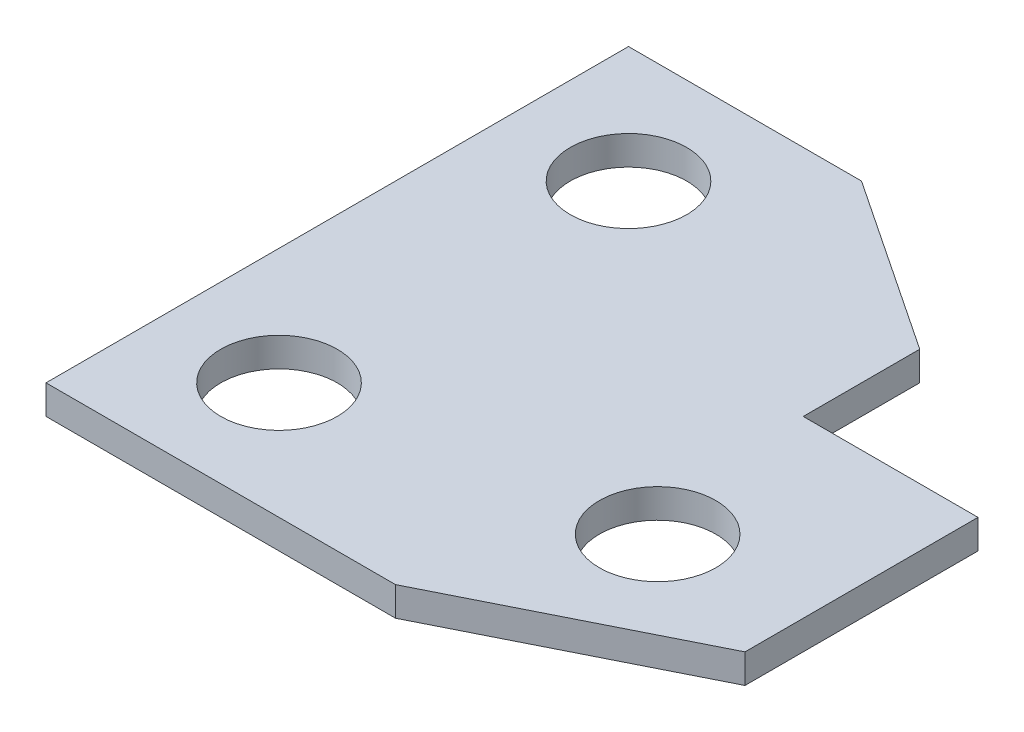
SolidWorks part; units mm, degrees
ref_plane "Front Plane" through (0, 0, 0) normal (0, 0, 1) x (1, 0, 0)
ref_plane "Top Plane" through (0, 0, 0) normal (0, 1, 0) x (1, 0, 0)
ref_plane "Right Plane" through (0, 0, 0) normal (1, 0, 0) x (0, 0, -1)
sketch "Sketch1" plane through (0, 0, 0) normal (0, 1, 0) x (1, 0, 0)
  line L0 (0, 0) -> (60, 0)
  line L2 (0, 0) -> (0, 100)
  line L3 (0, 100) -> (40, 100)
  line L7 (70, 60) -> (100, 60)
  line L8 (100, 20) -> (100, 60)
  line L9 (100, 20) -> (60, 0)
  line L10 (70, 60) -> (70, 80)
  line L11 (40, 100) -> (70, 80)
  line L12 (20, 75.7272) -> (20, 30.993) construction
  circle A0 centre (20, 80) radius 10
  circle A1 centre (20, 20) radius 10
  circle A2 centre (75, 30) radius 10
  point P8 (100, 20)
  dimension "D12" = 20
  dimension "D1" = 100
  dimension "D2" = 40
  dimension "D3" = 100
  dimension "D4" = 60
  dimension "D5" = 60
  dimension "D6" = 20
  dimension "D7" = 70
  dimension "D8" = 20
  dimension "D9" = 20
  dimension "D10" = 60
  dimension "D11" = 20
  dimension "D13" = 75
  dimension "D14" = 30
extrude "Boss-Extrude1" add sketch "Sketch1" along normal blind 5
